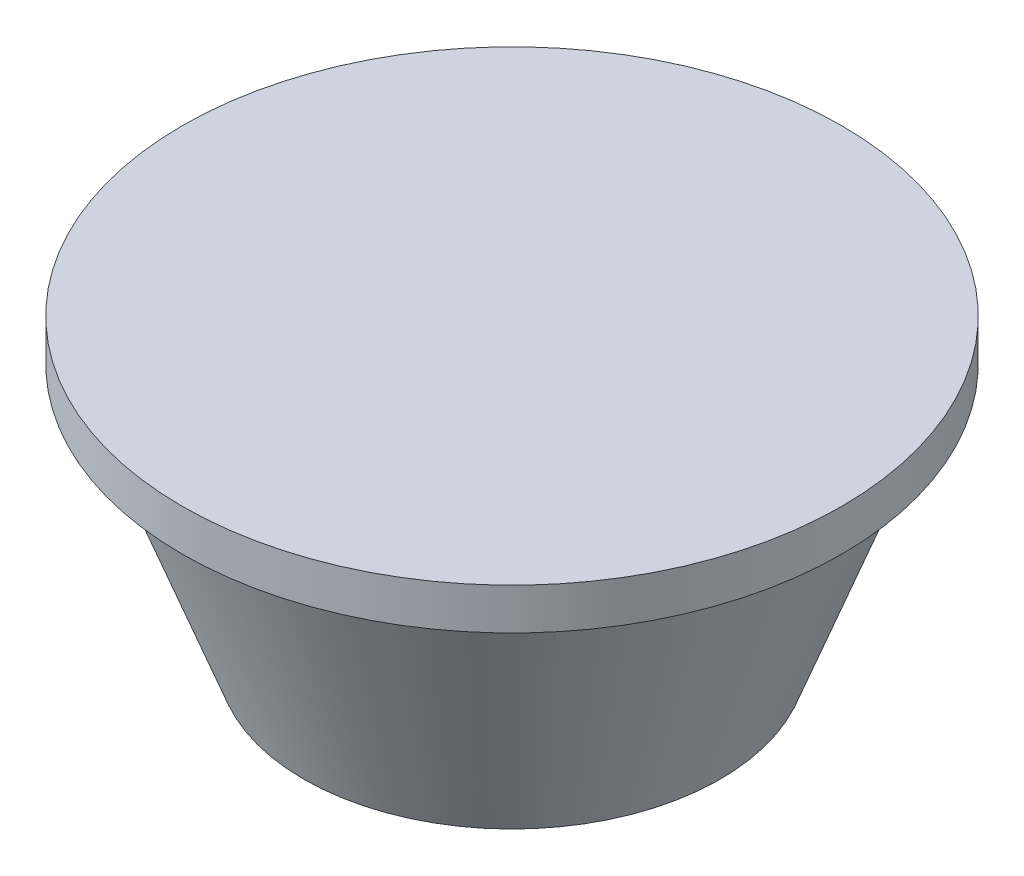
SolidWorks part; units mm, degrees
ref_plane "Front Plane" through (0, 0, 0) normal (0, 0, 1) x (1, 0, 0)
ref_plane "Top Plane" through (0, 0, 0) normal (0, 1, 0) x (1, 0, 0)
ref_plane "Right Plane" through (0, 0, 0) normal (1, 0, 0) x (0, 0, -1)
sketch "Sketch1" plane through (0, 0, 0) normal (1, 0, 0) x (0, 0, -1)
  line L0 (0, 2) -> (0, 0)
  line L1 (0, 0) -> (30, 0)
  line L2 (30, 0) -> (45, 40)
  line L3 (45, 40) -> (42.864, 40)
  line L4 (42.864, 40) -> (28.614, 2)
  line L5 (28.614, 2) -> (0, 2)
  point P0 (0, 1)
  dimension "D1" = 40
  dimension "D2" = 30
  dimension "D3" = 45
  dimension "D4" = 2
  dimension "D5" = 2
revolve "Revolve1" add sketch "Sketch1" angle 360 about L0
sketch "Sketch2" plane through (0, 0, 0) normal (1, 0, 0) x (0, 0, -1)
  line L0 (47.5, 42.8) -> (0, 42.8)
  line L5 (0, 40.3) -> (45.6, 40.3)
  line L6 (45.6, 40.3) -> (44.3, 36.8333)
  line L7 (44.3, 36.8333) -> (47.5, 36.8333)
  line L8 (47.5, 36.8333) -> (47.5, 42.8)
  line L9 (30, 0) -> (45, 40) construction
  line L10 (0, 40.3) -> (0, 42.8)
  dimension "D1" = 47.5
  dimension "D2" = 45.6
  dimension "D3" = 2.5
  dimension "D4" = 3.2
  dimension "D5" = 40.3
revolve "Revolve2" add sketch "Sketch2" angle 360 about L10
